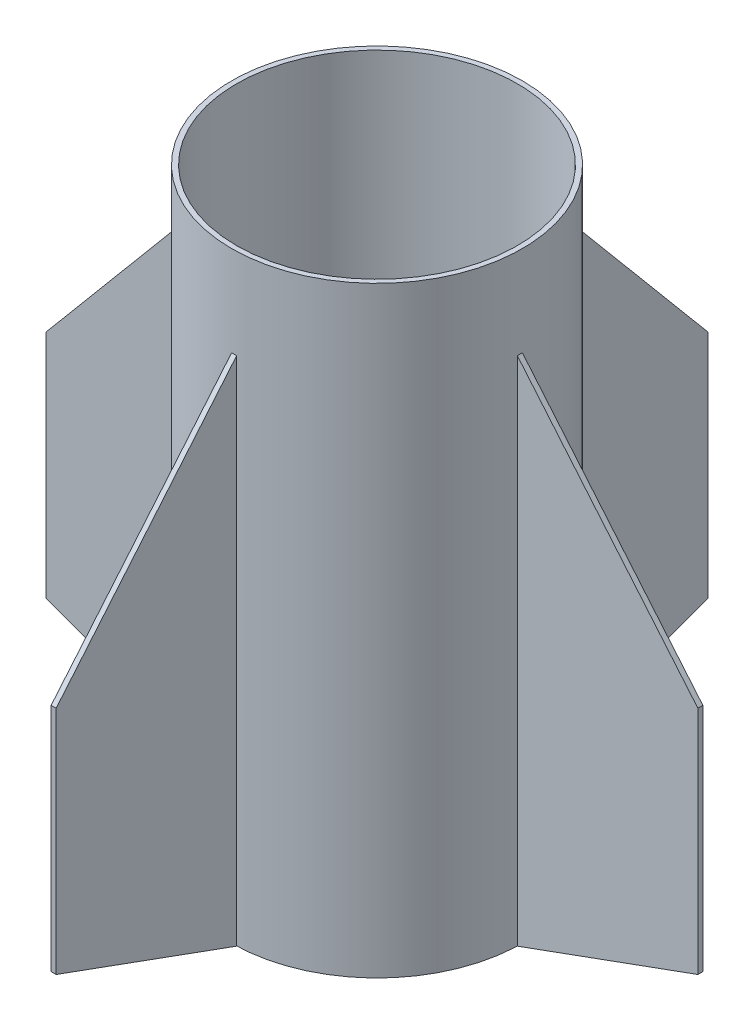
SolidWorks part; units mm, degrees
material "6061-T6 (SS)"
ref_plane "Front Plane" through (0, 0, 0) normal (0, 0, 1) x (1, 0, 0)
ref_plane "Top Plane" through (0, 0, 0) normal (0, 1, 0) x (1, 0, 0)
ref_plane "Right Plane" through (0, 0, 0) normal (1, 0, 0) x (0, 0, -1)
sketch "Sketch1" plane through (0, 0, 0) normal (0, 1, 0) x (1, 0, 0)
  circle A0 centre (0, 0) radius 88.9
  circle A1 centre (0, 0) radius 92.075
  dimension "D1" = 177.8
  dimension "D2" = 184.15
extrude "Boss-Extrude1" add sketch "Sketch1" along normal blind 381
sketch "Sketch2" plane through (0, 0, 0) normal (1, 0, 0) x (0, 0, -1)
  line L0 (-92.075, 323.85) -> (-206.375, 187.6577)
  line L1 (-92.075, 381) -> (-92.075, 0) construction
  line L2 (-206.375, 187.6577) -> (-206.375, 41.6077)
  line L3 (-206.375, 41.6077) -> (-92.075, 0)
  line L4 (-92.075, 0) -> (-92.075, 323.85)
  line L5 (0, 0) -> (0, 544.109) construction
  dimension "D1" = 114.3
  dimension "D2" = 177.8
  dimension "D3" = 323.85
  dimension "D4" = 146.05
extrude "Boss-Extrude2" add sketch "Sketch2" along normal blind 3.175 separate body
sketch "Sketch5" plane through (0, 0, 0) normal (1, 0, 0) x (0, 0, -1)
  line L0 (92.075, 323.85) -> (206.375, 187.6577)
  line L1 (92.075, 0) -> (92.075, 381) construction
  line L2 (206.375, 187.6577) -> (206.375, 41.6077)
  line L3 (206.375, 41.6077) -> (92.075, 0)
  line L4 (92.075, 0) -> (92.075, 381) construction
  line L5 (92.075, 323.85) -> (92.075, 0)
  dimension "D1" = 323.85
  dimension "D2" = 177.8
  dimension "D3" = 114.3
  dimension "D4" = 146.05
extrude "Boss-Extrude3" add sketch "Sketch5" along normal blind 3.175 separate body
sketch "Sketch6" plane through (0, 0, 0) normal (0, 0, 1) x (1, 0, 0)
  line L0 (-92.075, 323.85) -> (-206.375, 187.6577)
  line L1 (-92.075, 381) -> (-92.075, 0) construction
  line L2 (-206.375, 187.6577) -> (-206.375, 41.6077)
  line L3 (-206.375, 41.6077) -> (-92.075, 0)
  line L4 (-92.075, 323.85) -> (-92.075, 0)
  dimension "D1" = 146.05
  dimension "D2" = 177.8
  dimension "D3" = 323.85
  dimension "D4" = 114.3
extrude "Boss-Extrude4" add sketch "Sketch6" along normal blind 3.175 separate body
sketch "Sketch7" plane through (0, 0, 0) normal (0, 0, 1) x (1, 0, 0)
  line L0 (92.075, 323.85) -> (206.375, 187.6577)
  line L1 (92.075, 0) -> (92.075, 381) construction
  line L2 (206.375, 187.6577) -> (206.375, 41.6077)
  line L3 (206.375, 41.6077) -> (92.075, 0)
  line L4 (92.075, 0) -> (92.075, 323.85)
  dimension "D1" = 114.3
  dimension "D2" = 146.05
  dimension "D3" = 177.8
  dimension "D4" = 323.85
extrude "Boss-Extrude5" add sketch "Sketch7" along normal blind 3.175 separate body
